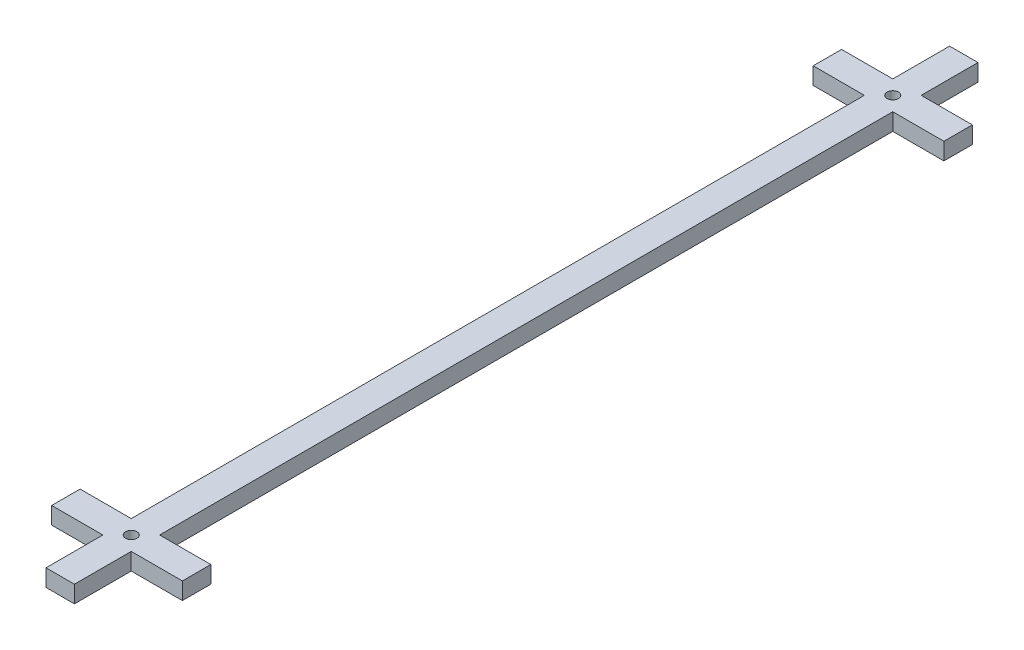
SolidWorks part; units mm, degrees
ref_plane "Front" through (0, 0, 0) normal (0, 0, 1) x (1, 0, 0)
ref_plane "Top" through (0, 0, 0) normal (0, 1, 0) x (1, 0, 0)
ref_plane "Right" through (0, 0, 0) normal (1, 0, 0) x (0, 0, -1)
sketch "Sketch3" plane through (0, 0, 0) normal (0, 1, 0) x (1, 0, 0)
  line L1 (-9, 15) -> (14, 15)
  line L2 (-9, 15) -> (-9, 10)
  line L3 (-9, 10) -> (14, 10)
  line L4 (14, 15) -> (14, 10)
  line L5 (-9, 149) -> (14, 149)
  line L6 (-9, 149) -> (-9, 144)
  line L7 (-9, 144) -> (14, 144)
  line L8 (14, 149) -> (14, 144)
  point P4 (0, 0)
  point P5 (0, 0)
  point P6 (0, 0)
  point P7 (0, 0)
  point P12 (0, 0)
  point P13 (0, 0)
  point P14 (-9.451, 14.9957)
  point P15 (0, 0)
  point P16 (0, 0)
  point P17 (0, 0)
  point P18 (0, 0)
  point P19 (0, 0)
  point P20 (0, 0)
  point P21 (0, 0)
  point P22 (0, 0)
  point P23 (0, 0)
sketch "Sketch1" plane through (0, 0, 0) normal (0, 1, 0) x (1, 0, 0)
  line L1 (0, 0) -> (5, 0)
  line L2 (0, 0) -> (0, 159)
  line L3 (0, 159) -> (5, 159)
  line L4 (5, 0) -> (5, 159)
  point P4 (0, 0)
  point P5 (0, 0)
extrude "Boss-Extrude1" add sketch "Sketch1" along normal blind 3
extrude "Boss-Extrude2" add sketch "Sketch3" along normal blind 3
sketch "Sketch5" plane through (0, 0, 0) normal (0, 1, 0) x (1, 0, 0)
  circle A0 centre (2.5, 12.5) radius 1
  circle A1 centre (2.5, 146.5) radius 1
  point P2 (0, 0)
extrude "Cut-Extrude4" cut sketch "Sketch5" along normal blind 3
